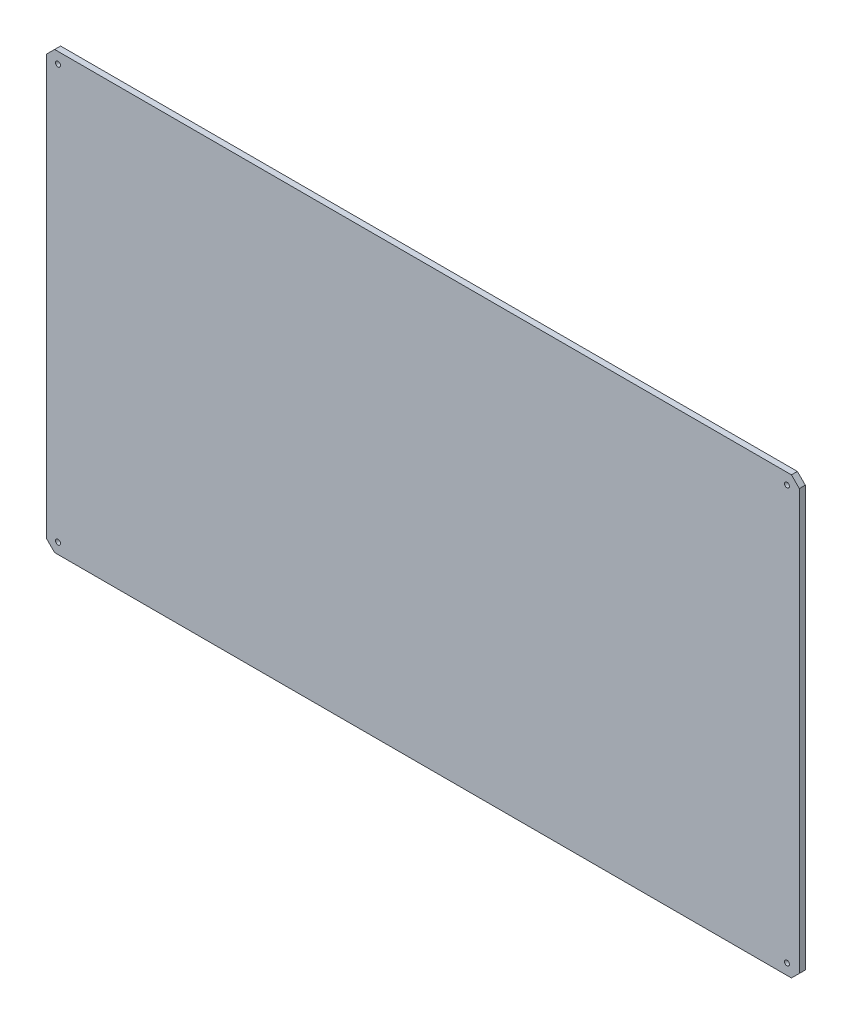
SolidWorks part; units mm, degrees
ref_plane "Front Plane" through (0, 0, 0) normal (0, 0, 1) x (1, 0, 0)
ref_plane "Top Plane" through (0, 0, 0) normal (0, 1, 0) x (1, 0, 0)
ref_plane "Right Plane" through (0, 0, 0) normal (1, 0, 0) x (0, 0, -1)
sketch "Sketch1" plane through (0, 0, 0) normal (0, 0, 1) x (1, 0, 0)
  line L1 (200, -110) -> (-180, -110)
  line L2 (200, -110) -> (200, 110)
  line L3 (200, 110) -> (-180, 110)
  line L4 (-180, -110) -> (-180, 110)
  line L7 (-180, 0) -> (200, 0) construction
  point P0 (0, 0)
  dimension "D1" = 380
  dimension "D2" = 220
extrude "Boss-Extrude1" add sketch "Sketch1" along normal blind 3
sketch "Sketch2" plane through (0, 0, 3) normal (0, 0, 1) x (1, 0, 0)
  circle A0 centre (-174.2783, -104.5607) radius 1.25
  circle A1 centre (-174.2783, 104.4393) radius 1.25
  circle A2 centre (193.7217, -104.5607) radius 1.25
  circle A3 centre (193.7217, 104.4393) radius 1.25
extrude "Cut-Extrude1" cut sketch "Sketch2" against normal blind 10
chamfer "Chamfer1" distance 4 angle 45 4 edges at (-180, -110, 1.5) (200, -110, 1.5) (200, 110, 1.5) (-180, 110, 1.5)
